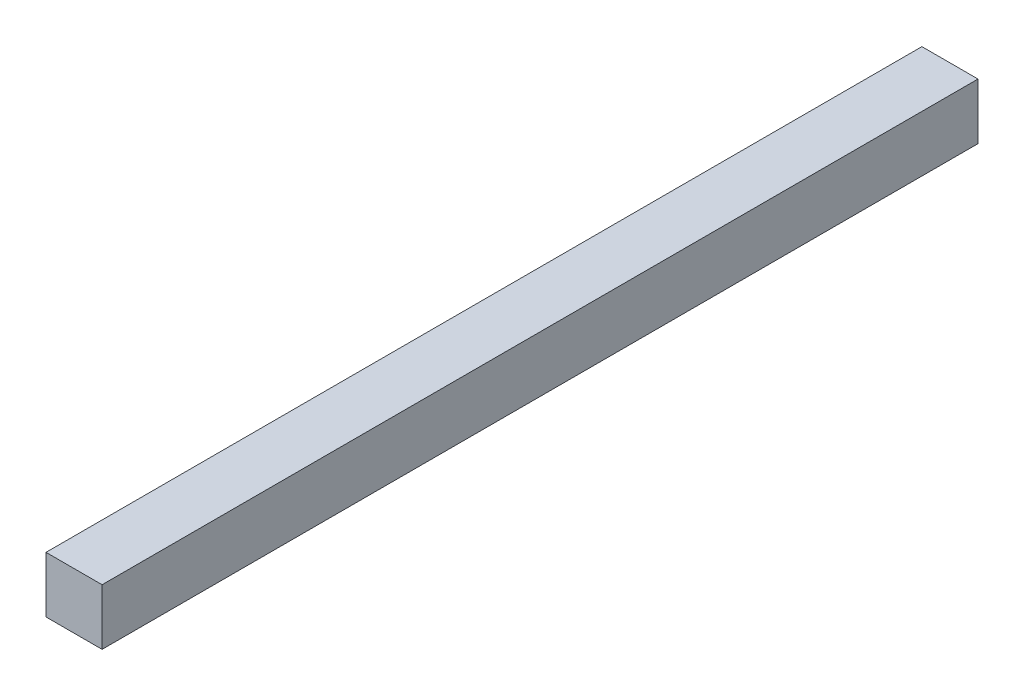
SolidWorks part; units mm, degrees
ref_plane "Front Plane" through (0, 0, 0) normal (0, 0, 1) x (1, 0, 0)
ref_plane "Top Plane" through (0, 0, 0) normal (0, 1, 0) x (1, 0, 0)
ref_plane "Right Plane" through (0, 0, 0) normal (1, 0, 0) x (0, 0, -1)
ref_plane "Plane1" through (0, 0, 173.0366) normal (0, 0, 1) x (1, 0, 0)
sketch "Sketch1" plane through (0, 0, 173.0366) normal (0, 0, 1) x (1, 0, 0)
  line B0 (-163.6075, 4.1993) -> (-133.5052, 4.1993)
  line B1 (-163.6075, 4.1993) -> (-163.6075, -25.8462)
  line B2 (-163.6075, -25.8462) -> (-133.5052, -25.8462)
  line B3 (-133.5052, 4.1993) -> (-133.5052, -25.8462)
sketch_block_instance "Block1-1"
sketch_block "Block1"
extrude "Boss-Extrude1" add sketch "Sketch1" against normal blind 470
